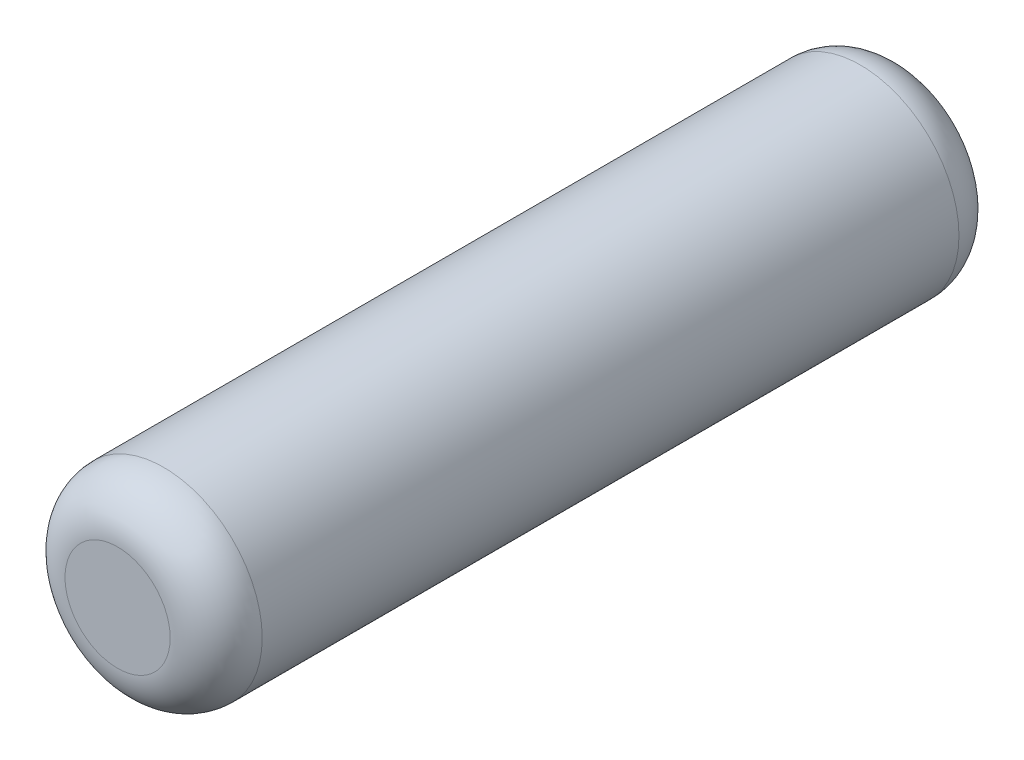
SolidWorks part; units mm, degrees
ref_plane "Front" through (0, 0, 0) normal (0, 0, 1) x (1, 0, 0)
ref_plane "Top" through (0, 0, 0) normal (0, 1, 0) x (1, 0, 0)
ref_plane "Right" through (0, 0, 0) normal (1, 0, 0) x (0, 0, -1)
sketch "Sketch1" plane through (0, 0, 0) normal (0, 0, 1) x (1, 0, 0)
  circle A0 centre (0, 0) radius 0.75
  dimension "D1" = 1.5
extrude "Boss-Extrude1" add sketch "Sketch1" along normal mid plane 6
fillet "Fillet1" radius 0.35 2 edges at (0.75, 0, -3) (0.75, 0, 3)
